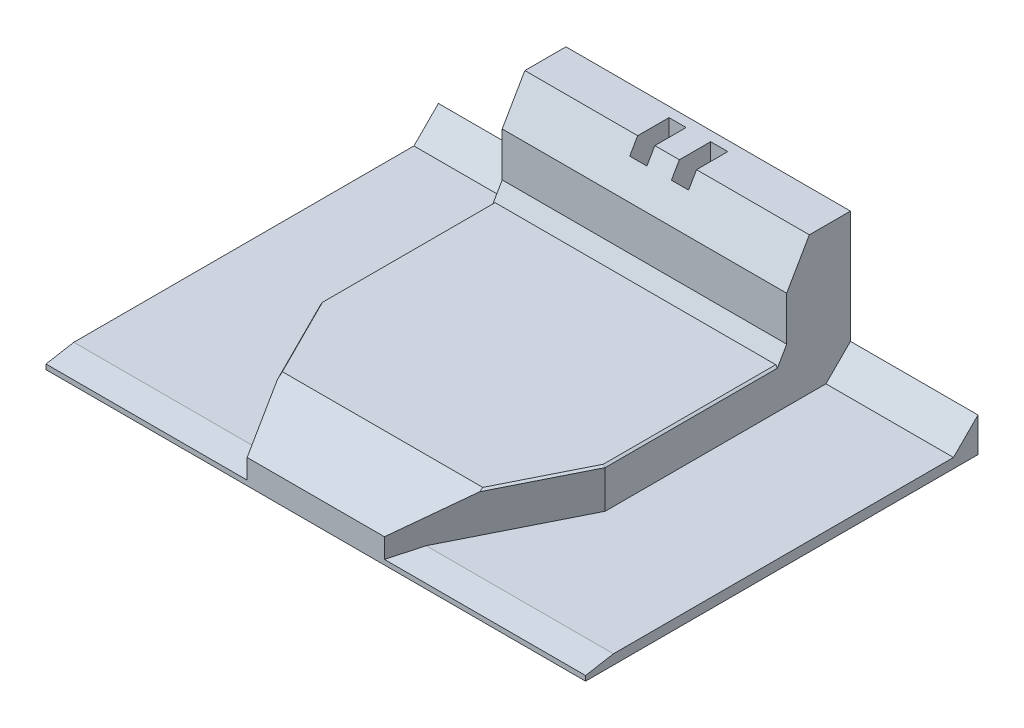
SolidWorks part; units mm, degrees
ref_plane "Front" through (0, 0, 0) normal (0, 0, 1) x (1, 0, 0)
ref_plane "Top" through (0, 0, 0) normal (0, 1, 0) x (1, 0, 0)
ref_plane "Right" through (0, 0, 0) normal (1, 0, 0) x (0, 0, -1)
sketch "草图1" plane through (0, 0, 0) normal (0, 1, 0) x (1, 0, 0)
  line L1 (55, -40) -> (-55, -40)
  line L2 (55, -40) -> (55, 40)
  line L3 (55, 40) -> (-55, 40)
  line L4 (-55, -40) -> (-55, 40)
  line L5 (55, -40) -> (-55, 40) construction
  line L6 (55, 40) -> (-55, -40) construction
  point P0 (0, 0)
  dimension "D1" = 80
  dimension "D2" = 110
extrude "凸台-拉伸1" add sketch "草图1" along normal blind 2
sketch "草图2" plane through (0, 2, 0) normal (0, 1, 0) x (1, 0, 0)
  line L0 (55, 40) -> (-55, 40) construction
  line L1 (29, -40) -> (-29, -40)
  line L2 (29, -40) -> (29, 40)
  line L3 (29, 40) -> (-29, 40)
  line L4 (-29, -40) -> (-29, 40)
  line L5 (29, -40) -> (-29, 40) construction
  line L6 (29, 40) -> (-29, -40) construction
  point P0 (0, 0)
  dimension "D1" = 58
extrude "凸台-拉伸2" add sketch "草图2" along normal blind 8
sketch "草图3" plane through (0, 10, 0) normal (0, 1, 0) x (1, 0, 0)
  line L0 (0, 48.7805) -> (0, -54.6542) construction
  line L1 (-14, -40) -> (-29, -10)
  line L2 (-29, -40) -> (29, -40) construction
  line L3 (-29, 40) -> (-29, -40) construction
  line L4 (-29, -10) -> (-29, -40)
  line L5 (-29, -40) -> (-14, -40)
  line L6 (29, -40) -> (14, -40)
  line L7 (29, -10) -> (29, -40)
  line L8 (14, -40) -> (29, -10)
  dimension "D1" = 30
  dimension "D2" = 15
extrude "切除-拉伸1" cut sketch "草图3" against normal up to surface (8 mm away) up to face at (-42, 2, 0)
sketch "草图4" plane through (0, 2, 0) normal (0, 1, 0) x (1, 0, 0)
  line L0 (0, 80.3318) -> (0, -50.6251) construction
  line L1 (29, 40) -> (-29, 40) construction
  line L2 (29, 27) -> (-29, 27)
  line L3 (29, 27) -> (29, 40)
  line L4 (29, 40) -> (-29, 40)
  line L5 (-29, 27) -> (-29, 40)
  line L6 (29, 27) -> (-29, 40) construction
  line L7 (29, 40) -> (-29, 27) construction
  line L8 (-29, 40) -> (-29, -10) construction
  point P3 (0, 33.5)
  dimension "D1" = 13
extrude "凸台-拉伸3" add sketch "草图4" along normal blind 28
chamfer "倒角1" distance 8 angle 30 1 edges at (0, 30, -27)
chamfer "倒角2" distance 5 angle 70 1 edges at (0, 10, 40)
chamfer "倒角3" distance 1 angle 80 2 edges at (34.5, 2, 40) (-34.5, 2, 40)
sketch "草图12" plane through (29, 0, 0) normal (1, 0, 0) x (0, 0, -1)
  line L0 (40, 2) -> (40, 7)
  line L1 (40, 30) -> (40, 2) construction
  line L2 (40, 7) -> (35, 2)
  line L3 (-10, 2) -> (40, 2) construction
  line L4 (35, 2) -> (40, 2)
  dimension "D1" = 5
  dimension "D2" = 5
extrude "凸台-拉伸5" add sketch "草图12" along normal up to surface and the other way up to surface up to face at (55, 1, 6.8657) other way up to face at (-55, 1, 6.8657)
sketch "草图5" plane through (0, 0, 0) normal (0, -1, 0) x (1, 0, 0)
  line L0 (0, 87.2176) -> (0, -65.4747) construction
  line L2 (-2.5, -38) -> (-6, -38)
  line L3 (-2.5, -38) -> (-2.5, -30)
  line L4 (-2.5, -30) -> (-6, -30)
  line L5 (-6, -38) -> (-6, -30)
  line L6 (-2.5, -38) -> (-6, -30) construction
  line L7 (-2.5, -30) -> (-6, -38) construction
  line L8 (2.5, -30) -> (6, -38) construction
  line L9 (2.5, -38) -> (6, -30) construction
  line L10 (6, -38) -> (6, -30)
  line L11 (2.5, -30) -> (6, -30)
  line L12 (2.5, -38) -> (2.5, -30)
  line L13 (2.5, -38) -> (6, -38)
  line L14 (55, -40) -> (-55, -40) construction
  point P3 (-4.25, -34)
  point P8 (-2.5, -34)
  point P15 (4.25, -34)
  dimension "D1" = 3.5
  dimension "D2" = 8
  dimension "D3" = 2
  dimension "D4" = 8.5
extrude "切除-拉伸2" cut sketch "草图5" against normal through all
sketch "草图6" plane through (0, 0, 0) normal (0, -1, 0) x (1, 0, 0)
  line L0 (2.5, -38) -> (6, -38) construction
  line L1 (15, -38) -> (-15, -38)
  line L2 (15, -38) -> (15, -18)
  line L3 (15, -18) -> (-15, -18)
  line L4 (-15, -38) -> (-15, -18)
  line L5 (15, -38) -> (-15, -18) construction
  line L6 (15, -18) -> (-15, -38) construction
  line L7 (0, 11.1105) -> (0, -52.9192) construction
  point P0 (0, -28)
  dimension "D1" = 20
  dimension "D2" = 30
extrude "切除-拉伸3" cut sketch "草图6" against normal blind 9
sketch "草图7" plane through (0, 9, 0) normal (0, -1, 0) x (1, 0, 0)
  line L0 (0, 13.33) -> (0, -44.95) construction
  line L2 (15, -29) -> (-15, -29)
  line L3 (15, -29) -> (15, -26)
  line L4 (15, -26) -> (-15, -26)
  line L5 (-15, -29) -> (-15, -26)
  line L6 (15, -29) -> (-15, -26) construction
  line L7 (15, -26) -> (-15, -29) construction
  line L8 (-6, -30) -> (-2.5, -30) construction
  line L9 (-15, -18) -> (-15, -38) construction
  point P3 (0, -27.5)
  dimension "D1" = 3
  dimension "D3" = 1
extrude "凸台-拉伸4" add sketch "草图7" along normal blind 4
sketch "草图8" plane through (0, 5, 0) normal (0, -1, 0) x (1, 0, 0)
  line L0 (0, 8.0257) -> (0, -44.3237) construction
  line L7 (15, -26) -> (-15, -26) construction
  line L8 (-3, -29) -> (-5.5, -29)
  line L9 (-3, -29) -> (-3, -26)
  line L10 (-3, -26) -> (-5.5, -26)
  line L11 (-5.5, -29) -> (-5.5, -26)
  line L12 (-3, -29) -> (-5.5, -26) construction
  line L13 (-3, -26) -> (-5.5, -29) construction
  line L14 (-15, -29) -> (15, -29) construction
  line L15 (3, -26) -> (5.5, -29) construction
  line L16 (3, -29) -> (5.5, -26) construction
  line L17 (5.5, -29) -> (5.5, -26)
  line L18 (3, -26) -> (5.5, -26)
  line L19 (3, -29) -> (3, -26)
  line L20 (3, -29) -> (5.5, -29)
  point P3 (-4.25, -27.5)
  point P16 (4.25, -27.5)
  dimension "D1" = 2.5
  dimension "D2" = 8.5
extrude "切除-拉伸4" cut sketch "草图8" against normal blind 0.2
sketch "草图10" plane through (0, 5, 0) normal (0, -1, 0) x (1, 0, 0)
  line L0 (0, -7.9787) -> (0, -48.3384) construction
  line L1 (-5.5, -26) -> (-15, -26) construction
  circle A0 centre (-8, -27.5) radius 0.5
  circle A1 centre (8, -27.5) radius 0.5
  circle A2 centre (0, -27.5) radius 0.5
  dimension "D1" = 1
  dimension "D4" = 1
  dimension "D2" = 1.5
  dimension "D3" = 16
extrude "切除-拉伸5" cut sketch "草图10" against normal blind 4
sketch "草图11" plane through (0, 0, -40) normal (0, 0, -1) x (-1, 0, 0)
  line L0 (0, 39.9418) -> (0, -9.4441) construction
  line L2 (-55, 0) -> (55, 0) construction
  circle A0 centre (-52.5, 2) radius 0.5
  circle A1 centre (52.5, 2) radius 0.5
  circle A2 centre (-27, 28) radius 0.5
  circle A3 centre (27, 28) radius 0.5
  dimension "D1" = 1
  dimension "D4" = 1
  dimension "D2" = 2
  dimension "D3" = 105
  dimension "D5" = 54
  dimension "D6" = 26
extrude "切除-拉伸6" cut sketch "草图11" against normal blind 4
chamfer "倒角4" distance 3 angle 30 1 edges at (0, 10, -27)
chamfer "倒角5" distance 0.5 angle 30 4 edges at (-24.9343, 10, 18.1313) (-29, 10, -7.634) (29, 10, -7.634) (24.9343, 10, 18.1313)
sketch "草图13" plane through (0, 0, 0) normal (0, -1, 0) x (1, 0, 0)
  line L0 (0, 43.9932) -> (0, -16.296) construction
  line L1 (27.5, -16) -> (-27.5, -16)
  line L2 (27.5, -16) -> (27.5, 9.6713)
  line L4 (-27.5, -16) -> (-27.5, 9.6713)
  line L5 (27.5, -16) -> (-27.5, 9.6713) construction
  line L6 (27.5, 9.6713) -> (-27.5, -16) construction
  line L7 (15, -18) -> (-15, -18) construction
  line L8 (-27.5, 9.6713) -> (-14.5, 30)
  line L9 (-55, 45.6713) -> (-11.1644, 45.6713) construction
  line L10 (-14.5, 30) -> (14.5, 30)
  line L11 (-55, 40) -> (55, 40) construction
  line L12 (27.5, 9.6713) -> (14.5, 30)
  point P0 (0, -3.1644)
  point P17 (0, 40)
  dimension "D1" = 55
  dimension "D2" = 2
  dimension "D3" = 36
  dimension "D4" = 10
  dimension "D5" = 29
extrude "切除-拉伸7" cut sketch "草图13" against normal blind 8
sketch "草图14" plane through (0, 0, -40) normal (0, 0, -1) x (-1, 0, 0)
  line L0 (-55, 0) -> (55, 0) construction
  line L1 (2.5, -5) -> (-2.5, -5)
  line L2 (2.5, -5) -> (2.5, 5)
  line L3 (2.5, 5) -> (-2.5, 5)
  line L4 (-2.5, -5) -> (-2.5, 5)
  line L5 (2.5, -5) -> (-2.5, 5) construction
  line L6 (2.5, 5) -> (-2.5, -5) construction
  point P0 (0, 0)
  dimension "D1" = 5
  dimension "D2" = 5
extrude "切除-拉伸8" cut sketch "草图14" against normal blind 3
sketch "草图15" plane through (0, 2, 0) normal (0, 1, 0) x (1, 0, 0)
  line L0 (-29, 35) -> (-55, 35) construction
  line L1 (-51, -32.3287) -> (-53, -32.3287)
  line L2 (-51, -32.3287) -> (-51, 33)
  line L3 (-51, 33) -> (-53, 33)
  line L4 (-53, -32.3287) -> (-53, 33)
  line L5 (-51, -32.3287) -> (-53, 33) construction
  line L6 (-51, 33) -> (-53, -32.3287) construction
  line L7 (-55, 35) -> (-55, -34.3287) construction
  line L8 (-55, -34.3287) -> (-16.8356, -34.3287) construction
  line L9 (-47, -32.3287) -> (-49, -32.3287)
  line L10 (-47, -32.3287) -> (-47, 33)
  line L11 (-47, 33) -> (-49, 33)
  line L12 (-49, -32.3287) -> (-49, 33)
  line L13 (-47, -32.3287) -> (-49, 33) construction
  line L14 (-47, 33) -> (-49, -32.3287) construction
  line L15 (-43, -32.3287) -> (-45, -32.3287)
  line L16 (-43, -32.3287) -> (-43, 33)
  line L17 (-43, 33) -> (-45, 33)
  line L18 (-45, -32.3287) -> (-45, 33)
  line L19 (-43, -32.3287) -> (-45, 33) construction
  line L20 (-43, 33) -> (-45, -32.3287) construction
  line L21 (-39, -32.3287) -> (-41, -32.3287)
  line L22 (-39, -32.3287) -> (-39, 33)
  line L23 (-39, 33) -> (-41, 33)
  line L24 (-41, -32.3287) -> (-41, 33)
  line L25 (-39, -32.3287) -> (-41, 33) construction
  line L26 (-39, 33) -> (-41, -32.3287) construction
  line L27 (-35, -32.3287) -> (-37, -32.3287)
  line L28 (-35, -32.3287) -> (-35, 33)
  line L29 (-35, 33) -> (-37, 33)
  line L30 (-37, -32.3287) -> (-37, 33)
  line L31 (-35, -32.3287) -> (-37, 33) construction
  line L32 (-35, 33) -> (-37, -32.3287) construction
  line L33 (-31, -32.3287) -> (-33, -32.3287)
  line L34 (-31, -32.3287) -> (-31, 33)
  line L35 (-31, 33) -> (-33, 33)
  line L36 (-33, -32.3287) -> (-33, 33)
  line L37 (-31, -32.3287) -> (-33, 33) construction
  line L38 (-31, 33) -> (-33, -32.3287) construction
  line L39 (0, 83.6273) -> (0, -68.813) construction
  line L40 (31, 33) -> (33, -32.3287) construction
  line L41 (31, -32.3287) -> (33, 33) construction
  line L42 (35, 33) -> (37, -32.3287) construction
  line L43 (35, -32.3287) -> (37, 33) construction
  line L44 (39, 33) -> (41, -32.3287) construction
  line L45 (39, -32.3287) -> (41, 33) construction
  line L46 (43, 33) -> (45, -32.3287) construction
  line L47 (43, -32.3287) -> (45, 33) construction
  line L48 (47, 33) -> (49, -32.3287) construction
  line L49 (47, -32.3287) -> (49, 33) construction
  line L50 (51, 33) -> (53, -32.3287) construction
  line L51 (51, -32.3287) -> (53, 33) construction
  line L52 (33, -32.3287) -> (33, 33)
  line L53 (31, 33) -> (33, 33)
  line L54 (31, -32.3287) -> (31, 33)
  line L55 (31, -32.3287) -> (33, -32.3287)
  line L56 (37, -32.3287) -> (37, 33)
  line L57 (35, 33) -> (37, 33)
  line L58 (35, -32.3287) -> (35, 33)
  line L59 (35, -32.3287) -> (37, -32.3287)
  line L60 (41, -32.3287) -> (41, 33)
  line L61 (39, 33) -> (41, 33)
  line L62 (39, -32.3287) -> (39, 33)
  line L63 (39, -32.3287) -> (41, -32.3287)
  line L64 (45, -32.3287) -> (45, 33)
  line L65 (43, 33) -> (45, 33)
  line L66 (43, -32.3287) -> (43, 33)
  line L67 (43, -32.3287) -> (45, -32.3287)
  line L68 (49, -32.3287) -> (49, 33)
  line L69 (47, 33) -> (49, 33)
  line L70 (47, -32.3287) -> (47, 33)
  line L71 (47, -32.3287) -> (49, -32.3287)
  line L72 (53, -32.3287) -> (53, 33)
  line L73 (51, 33) -> (53, 33)
  line L74 (51, -32.3287) -> (51, 33)
  line L75 (51, -32.3287) -> (53, -32.3287)
  point P0 (-52, 0.3356)
  point P13 (-48, 0.3356)
  point P18 (-44, 0.3356)
  point P23 (-40, 0.3356)
  point P28 (-36, 0.3356)
  point P33 (-32, 0.3356)
  point P63 (32, 0.3356)
  point P64 (36, 0.3356)
  point P65 (40, 0.3356)
  point P66 (44, 0.3356)
  point P67 (48, 0.3356)
  point P68 (52, 0.3356)
  dimension "D1" = 2
  dimension "D2" = 2
  dimension "D3" = 2
  dimension "D4" = 2
  dimension "D5" = 6
extrude "切除-拉伸9" [suppressed] cut sketch "草图15" against normal through all
sketch "草图16" plane through (0, 30, 0) normal (0, 1, 0) x (1, 0, 0)
  line L0 (0, 60.9434) -> (0, -15.7301) construction
  line L1 (-29, 35) -> (-29, 40) construction
  line L2 (-25, 33.1188) -> (-27, 33.1188)
  line L3 (-25, 33.1188) -> (-25, 38.5)
  line L4 (-25, 38.5) -> (-27, 38.5)
  line L5 (-27, 33.1188) -> (-27, 38.5)
  line L6 (-25, 33.1188) -> (-27, 38.5) construction
  line L7 (-25, 38.5) -> (-27, 33.1188) construction
  line L8 (29, 40) -> (-29, 40) construction
  line L9 (-29, 31.6188) -> (-6, 31.6188) construction
  line L10 (-22, 33.1188) -> (-24, 33.1188)
  line L11 (-22, 33.1188) -> (-22, 38.5)
  line L12 (-22, 38.5) -> (-24, 38.5)
  line L13 (-24, 33.1188) -> (-24, 38.5)
  line L14 (-22, 33.1188) -> (-24, 38.5) construction
  line L15 (-22, 38.5) -> (-24, 33.1188) construction
  line L16 (-19, 33.1188) -> (-21, 33.1188)
  line L17 (-19, 33.1188) -> (-19, 38.5)
  line L18 (-19, 38.5) -> (-21, 38.5)
  line L19 (-21, 33.1188) -> (-21, 38.5)
  line L20 (-19, 33.1188) -> (-21, 38.5) construction
  line L21 (-19, 38.5) -> (-21, 33.1188) construction
  line L22 (-16, 33.1188) -> (-18, 33.1188)
  line L23 (-16, 33.1188) -> (-16, 38.5)
  line L24 (-16, 38.5) -> (-18, 38.5)
  line L25 (-18, 33.1188) -> (-18, 38.5)
  line L26 (-16, 33.1188) -> (-18, 38.5) construction
  line L27 (-16, 38.5) -> (-18, 33.1188) construction
  line L28 (-13, 33.1188) -> (-15, 33.1188)
  line L29 (-13, 33.1188) -> (-13, 38.5)
  line L30 (-13, 38.5) -> (-15, 38.5)
  line L31 (-15, 33.1188) -> (-15, 38.5)
  line L32 (-13, 33.1188) -> (-15, 38.5) construction
  line L33 (-13, 38.5) -> (-15, 33.1188) construction
  line L34 (-10, 33.1188) -> (-12, 33.1188)
  line L35 (-10, 33.1188) -> (-10, 38.5)
  line L36 (-10, 38.5) -> (-12, 38.5)
  line L37 (-12, 33.1188) -> (-12, 38.5)
  line L38 (-10, 33.1188) -> (-12, 38.5) construction
  line L39 (-10, 38.5) -> (-12, 33.1188) construction
  line L40 (10, 38.5) -> (12, 33.1188) construction
  line L41 (10, 33.1188) -> (12, 38.5) construction
  line L42 (13, 38.5) -> (15, 33.1188) construction
  line L43 (13, 33.1188) -> (15, 38.5) construction
  line L44 (16, 38.5) -> (18, 33.1188) construction
  line L45 (16, 33.1188) -> (18, 38.5) construction
  line L46 (19, 38.5) -> (21, 33.1188) construction
  line L47 (19, 33.1188) -> (21, 38.5) construction
  line L48 (22, 38.5) -> (24, 33.1188) construction
  line L49 (22, 33.1188) -> (24, 38.5) construction
  line L50 (25, 38.5) -> (27, 33.1188) construction
  line L51 (25, 33.1188) -> (27, 38.5) construction
  line L52 (12, 33.1188) -> (12, 38.5)
  line L53 (10, 38.5) -> (12, 38.5)
  line L54 (10, 33.1188) -> (10, 38.5)
  line L55 (10, 33.1188) -> (12, 33.1188)
  line L56 (15, 33.1188) -> (15, 38.5)
  line L57 (13, 38.5) -> (15, 38.5)
  line L58 (13, 33.1188) -> (13, 38.5)
  line L59 (13, 33.1188) -> (15, 33.1188)
  line L60 (18, 33.1188) -> (18, 38.5)
  line L61 (16, 38.5) -> (18, 38.5)
  line L62 (16, 33.1188) -> (16, 38.5)
  line L63 (16, 33.1188) -> (18, 33.1188)
  line L64 (21, 33.1188) -> (21, 38.5)
  line L65 (19, 38.5) -> (21, 38.5)
  line L66 (19, 33.1188) -> (19, 38.5)
  line L67 (19, 33.1188) -> (21, 33.1188)
  line L68 (24, 33.1188) -> (24, 38.5)
  line L69 (22, 38.5) -> (24, 38.5)
  line L70 (22, 33.1188) -> (22, 38.5)
  line L71 (22, 33.1188) -> (24, 33.1188)
  line L72 (27, 33.1188) -> (27, 38.5)
  line L73 (25, 38.5) -> (27, 38.5)
  line L74 (25, 33.1188) -> (25, 38.5)
  line L75 (25, 33.1188) -> (27, 33.1188)
  point P3 (-26, 35.8094)
  point P16 (-23, 35.8094)
  point P21 (-20, 35.8094)
  point P26 (-17, 35.8094)
  point P31 (-14, 35.8094)
  point P36 (-11, 35.8094)
  point P63 (11, 35.8094)
  point P64 (14, 35.8094)
  point P65 (17, 35.8094)
  point P66 (20, 35.8094)
  point P67 (23, 35.8094)
  point P68 (26, 35.8094)
  dimension "D1" = 2
  dimension "D2" = 2
  dimension "D3" = 1.5
  dimension "D4" = 1.5
  dimension "D5" = 6
extrude "切除-拉伸10" [suppressed] cut sketch "草图16" against normal through all
sketch "草图17" plane through (0, 10, 0) normal (0, 1, 0) x (1, 0, 0)
  line L0 (28.5, 25.2679) -> (-28.7113, 25.2679) construction
  line L1 (-26.7113, -11.1124) -> (-25.5222, -11.1124)
  line L2 (-26.7113, -11.1124) -> (-26.7113, 23.2679)
  line L3 (-26.7113, 23.2679) -> (-25.5222, 23.2679)
  line L4 (-25.5222, -11.1124) -> (-25.5222, 23.2679)
  line L5 (-26.7113, -11.1124) -> (-25.5222, 23.2679) construction
  line L6 (-26.7113, 23.2679) -> (-25.5222, -11.1124) construction
  line L7 (-28.7113, 25.2679) -> (-28.7113, -9.9319) construction
  line L8 (-22.7113, -11.1124) -> (-21.5222, -11.1124)
  line L9 (-22.7113, -11.1124) -> (-22.7113, 23.2679)
  line L10 (-22.7113, 23.2679) -> (-21.5222, 23.2679)
  line L11 (-21.5222, -11.1124) -> (-21.5222, 23.2679)
  line L12 (-22.7113, -11.1124) -> (-21.5222, 23.2679) construction
  line L13 (-22.7113, 23.2679) -> (-21.5222, -11.1124) construction
  line L14 (-18.7113, -11.1124) -> (-17.5222, -11.1124)
  line L15 (-18.7113, -11.1124) -> (-18.7113, 23.2679)
  line L16 (-18.7113, 23.2679) -> (-17.5222, 23.2679)
  line L17 (-17.5222, -11.1124) -> (-17.5222, 23.2679)
  line L18 (-18.7113, -11.1124) -> (-17.5222, 23.2679) construction
  line L19 (-18.7113, 23.2679) -> (-17.5222, -11.1124) construction
  line L20 (-14.7113, -11.1124) -> (-13.5222, -11.1124)
  line L21 (-14.7113, -11.1124) -> (-14.7113, 23.2679)
  line L22 (-14.7113, 23.2679) -> (-13.5222, 23.2679)
  line L23 (-13.5222, -11.1124) -> (-13.5222, 23.2679)
  line L24 (-14.7113, -11.1124) -> (-13.5222, 23.2679) construction
  line L25 (-14.7113, 23.2679) -> (-13.5222, -11.1124) construction
  line L26 (-10.7113, -11.1124) -> (-9.5222, -11.1124)
  line L27 (-10.7113, -11.1124) -> (-10.7113, 23.2679)
  line L28 (-10.7113, 23.2679) -> (-9.5222, 23.2679)
  line L29 (-9.5222, -11.1124) -> (-9.5222, 23.2679)
  line L30 (-10.7113, -11.1124) -> (-9.5222, 23.2679) construction
  line L31 (-10.7113, 23.2679) -> (-9.5222, -11.1124) construction
  line L32 (-6.7113, -11.1124) -> (-5.5222, -11.1124)
  line L33 (-6.7113, -11.1124) -> (-6.7113, 23.2679)
  line L34 (-6.7113, 23.2679) -> (-5.5222, 23.2679)
  line L35 (-5.5222, -11.1124) -> (-5.5222, 23.2679)
  line L36 (-6.7113, -11.1124) -> (-5.5222, 23.2679) construction
  line L37 (-6.7113, 23.2679) -> (-5.5222, -11.1124) construction
  line L38 (-2.7113, -11.1124) -> (-1.5222, -11.1124)
  line L39 (-2.7113, -11.1124) -> (-2.7113, 23.2679)
  line L40 (-2.7113, 23.2679) -> (-1.5222, 23.2679)
  line L41 (-1.5222, -11.1124) -> (-1.5222, 23.2679)
  line L42 (-2.7113, -11.1124) -> (-1.5222, 23.2679) construction
  line L43 (-2.7113, 23.2679) -> (-1.5222, -11.1124) construction
  line L44 (0, 21.8523) -> (0, -16.5542) construction
  line L45 (2.7113, 23.2679) -> (1.5222, -11.1124) construction
  line L46 (2.7113, -11.1124) -> (1.5222, 23.2679) construction
  line L47 (6.7113, 23.2679) -> (5.5222, -11.1124) construction
  line L48 (6.7113, -11.1124) -> (5.5222, 23.2679) construction
  line L49 (10.7113, 23.2679) -> (9.5222, -11.1124) construction
  line L50 (10.7113, -11.1124) -> (9.5222, 23.2679) construction
  line L51 (14.7113, 23.2679) -> (13.5222, -11.1124) construction
  line L52 (14.7113, -11.1124) -> (13.5222, 23.2679) construction
  line L53 (18.7113, 23.2679) -> (17.5222, -11.1124) construction
  line L54 (18.7113, -11.1124) -> (17.5222, 23.2679) construction
  line L55 (22.7113, 23.2679) -> (21.5222, -11.1124) construction
  line L56 (22.7113, -11.1124) -> (21.5222, 23.2679) construction
  line L57 (26.7113, 23.2679) -> (25.5222, -11.1124) construction
  line L58 (26.7113, -11.1124) -> (25.5222, 23.2679) construction
  line L59 (1.5222, -11.1124) -> (1.5222, 23.2679)
  line L60 (2.7113, 23.2679) -> (1.5222, 23.2679)
  line L61 (2.7113, -11.1124) -> (2.7113, 23.2679)
  line L62 (2.7113, -11.1124) -> (1.5222, -11.1124)
  line L63 (5.5222, -11.1124) -> (5.5222, 23.2679)
  line L64 (6.7113, 23.2679) -> (5.5222, 23.2679)
  line L65 (6.7113, -11.1124) -> (6.7113, 23.2679)
  line L66 (6.7113, -11.1124) -> (5.5222, -11.1124)
  line L67 (9.5222, -11.1124) -> (9.5222, 23.2679)
  line L68 (10.7113, 23.2679) -> (9.5222, 23.2679)
  line L69 (10.7113, -11.1124) -> (10.7113, 23.2679)
  line L70 (10.7113, -11.1124) -> (9.5222, -11.1124)
  line L71 (13.5222, -11.1124) -> (13.5222, 23.2679)
  line L72 (14.7113, 23.2679) -> (13.5222, 23.2679)
  line L73 (14.7113, -11.1124) -> (14.7113, 23.2679)
  line L74 (14.7113, -11.1124) -> (13.5222, -11.1124)
  line L75 (17.5222, -11.1124) -> (17.5222, 23.2679)
  line L76 (18.7113, 23.2679) -> (17.5222, 23.2679)
  line L77 (18.7113, -11.1124) -> (18.7113, 23.2679)
  line L78 (18.7113, -11.1124) -> (17.5222, -11.1124)
  line L79 (21.5222, -11.1124) -> (21.5222, 23.2679)
  line L80 (22.7113, 23.2679) -> (21.5222, 23.2679)
  line L81 (22.7113, -11.1124) -> (22.7113, 23.2679)
  line L82 (22.7113, -11.1124) -> (21.5222, -11.1124)
  line L83 (25.5222, -11.1124) -> (25.5222, 23.2679)
  line L84 (26.7113, 23.2679) -> (25.5222, 23.2679)
  line L85 (26.7113, -11.1124) -> (26.7113, 23.2679)
  line L86 (26.7113, -11.1124) -> (25.5222, -11.1124)
  point P0 (-26.1168, 6.0778)
  point P11 (-22.1168, 6.0778)
  point P16 (-18.1168, 6.0778)
  point P21 (-14.1168, 6.0778)
  point P26 (-10.1168, 6.0778)
  point P31 (-6.1168, 6.0778)
  point P36 (-2.1168, 6.0778)
  point P70 (2.1168, 6.0778)
  point P71 (6.1168, 6.0778)
  point P72 (10.1168, 6.0778)
  point P73 (14.1168, 6.0778)
  point P74 (18.1168, 6.0778)
  point P75 (22.1168, 6.0778)
  point P76 (26.1168, 6.0778)
  dimension "D1" = 2
  dimension "D2" = 2
  dimension "D3" = 7
extrude "切除-拉伸11" [suppressed] cut sketch "草图17" against normal through all
